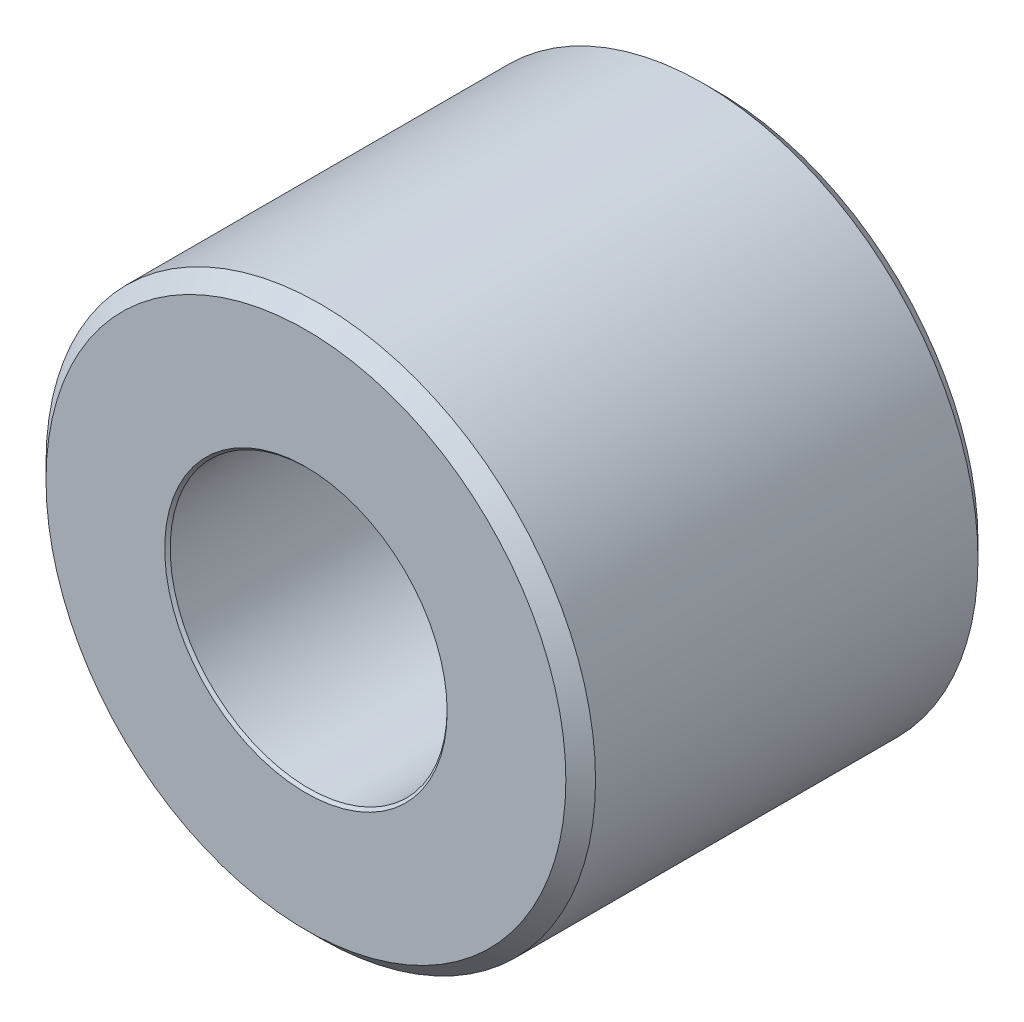
SolidWorks part; units mm, degrees
material "6061 Alloy"
ref_plane "Front Plane" through (0, 0, 0) normal (0, 0, 1) x (1, 0, 0)
ref_plane "Top Plane" through (0, 0, 0) normal (0, 1, 0) x (1, 0, 0)
ref_plane "Right Plane" through (0, 0, 0) normal (1, 0, 0) x (0, 0, -1)
sketch "Sketch1" plane through (0, 0, 0) normal (0, 0, 1) x (1, 0, 0)
  circle A0 centre (0, 0) radius 3.175 construction
  circle A1 centre (0, 0) radius 1.4605 construction
  point P4 (0, 3.175)
  dimension "ID" = 2.921
  dimension "OD" = 6.35
sketch "Sketch2" plane through (0, 0, 0) normal (1, 0, 0) x (0, 0, -1)
  line L0 (-2.3812, 3.175) -> (2.3812, 3.175) construction
  dimension "Length" = 4.7625
sketch "Sketch3" plane through (0, 0, 0) normal (0, 0, 1) x (1, 0, 0)
  circle A0 centre (0, 0) radius 1.4605 construction
  circle A1 centre (0, 0) radius 3.175 construction
  circle A2 centre (0, 0) radius 1.4605
  circle A3 centre (0, 0) radius 3.175
extrude "Boss-Extrude1" add sketch "Sketch3" against normal up to vertex (2.3813 mm away) and the other way up to vertex (2.3813 mm away) up to point (0, 3.175, -2.3812) other way up to point (0, 3.175, 2.3812)
chamfer "Chamfer1" distance 0.1714 angle 45 4 edges at (3.175, 0, 2.3812) (3.175, 0, -2.3812) (1.4605, 0, 2.3812) (1.4605, 0, -2.3812)
sketch "Sketch4" plane through (0, 0, 0) normal (0, 0, 1) x (1, 0, 0)
  circle A0 centre (0, 0) radius 1.6002
  dimension "D1" = 3.2004
extrude "Cut-Extrude1" cut sketch "Sketch4" against normal through all both and the other way through all
equation "\"D1@Chamfer1\"=(\"OD@Sketch1\"-\"ID@Sketch1\")*0.05"
